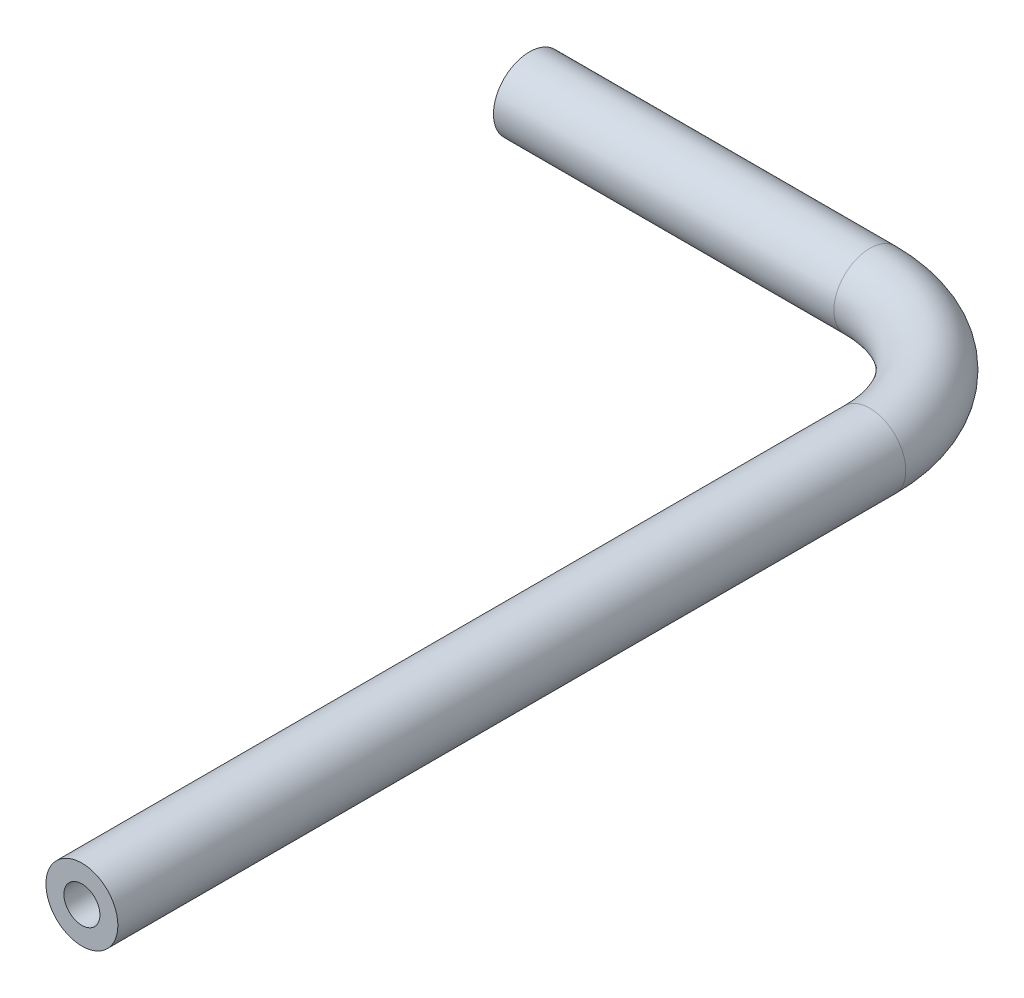
SolidWorks part; units mm, degrees
material "Nylon 101"
ref_plane "Front Plane" through (0, 0, 0) normal (0, 0, 1) x (1, 0, 0)
ref_plane "Top Plane" through (0, 0, 0) normal (0, 1, 0) x (1, 0, 0)
ref_plane "Right Plane" through (0, 0, 0) normal (1, 0, 0) x (0, 0, -1)
sketch "Sketch10" plane through (0, 0, 0) normal (0, 1, 0) x (1, 0, 0)
  line L0 (60.8594, -106.5557) -> (60.8594, -6.4079)
  line L1 (43.2668, 11.1847) -> (0, 11.1847)
  line L2 (0, -55) -> (0, 55) construction
  arc A0 (60.8594, -6.4079) -> (43.2668, 11.1847) centre (43.2668, -6.4079) ccw
  point P9 (0, 11.1847)
sketch "Sketch11" plane through (0, 0, 0) normal (1, 0, 0) x (0, 0, -1)
  circle A0 centre (11.1847, 0) radius 4.572
  circle A1 centre (11.1847, 0) radius 2.286
  dimension "D1" = 9.144
  dimension "D2" = 4.572
sweep "Sweep4" add profiles "Sketch11" path "Sketch10"
